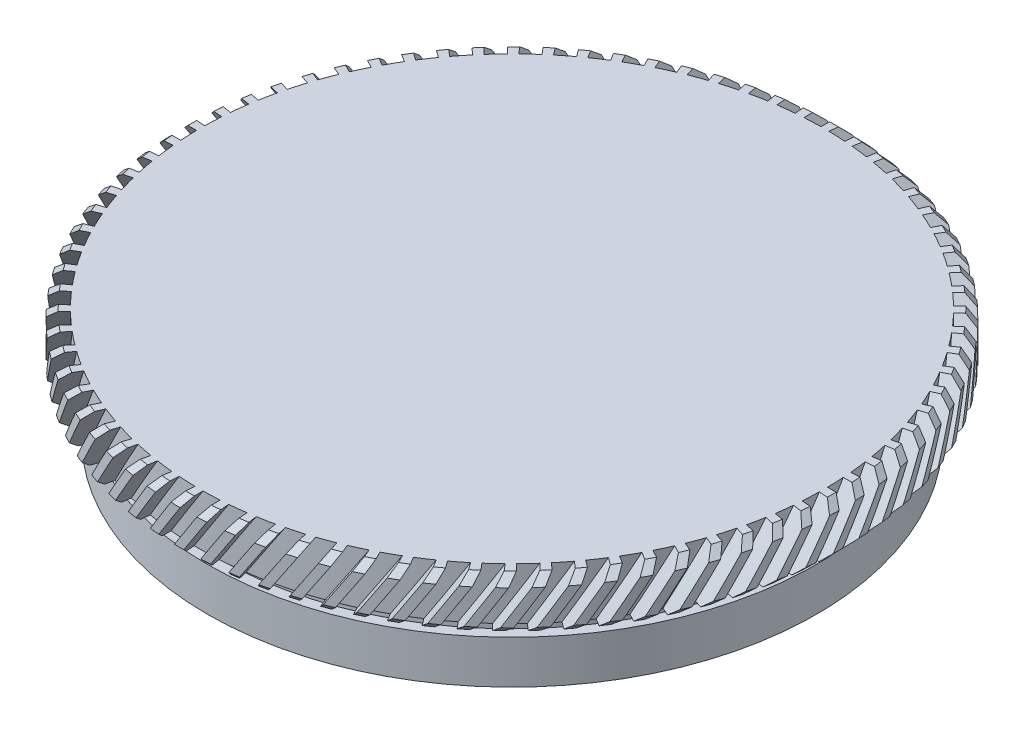
SolidWorks part; units mm, degrees
ref_plane "前视基准面" through (0, 0, 0) normal (0, 0, 1) x (1, 0, 0)
ref_plane "上视基准面" through (0, 0, 0) normal (0, 1, 0) x (1, 0, 0)
ref_plane "右视基准面" through (0, 0, 0) normal (1, 0, 0) x (0, 0, -1)
sketch "草图1" plane through (0, 0, 0) normal (0, 0, 1) x (1, 0, 0)
  line L0 (0, 66.6288) -> (0, -106.6399) construction
  line L1 (-97.6622, 0) -> (93.4292, 0) construction
  line L2 (0, 21.8713) -> (19.05, 21.8713)
  line L3 (19.05, 21.8713) -> (19.05, 18.8713)
  line L4 (17, 18.8713) -> (17, 17.8713)
  line L5 (17, 18.8713) -> (19.05, 18.8713)
  line L6 (17.6, 17.8713) -> (17.6, 15.3713)
  line L7 (17, 17.8713) -> (17.6, 17.8713)
  line L8 (15.75, 18.8713) -> (15.75, 15.3713)
  line L9 (0, 21.8713) -> (0, 18.8713)
  line L10 (15.75, 15.3713) -> (17.6, 15.3713)
  line L11 (0, 18.8713) -> (15.75, 18.8713)
  dimension "D1" = 19.05
  dimension "D2" = 3
  dimension "D3" = 17
  dimension "D4" = 17.6
  dimension "D5" = 15.75
  dimension "D6" = 1
  dimension "D7" = 2.5
revolve "旋转2" add sketch "草图1" angle 360 about L0
cosmetic thread "装饰螺纹线1" parameters "D2"=35
chamfer "倒角1" distance 0.5 angle 45 2 edges at (0, 21.8713, 19.05) (0, 18.8713, 19.05)
sketch "草图2" plane through (0, 0, 0) normal (0, 0, 1) x (1, 0, 0)
  line L0 (1.1082, 23.3033) -> (-5.3395, 13.2735)
  line L1 (1.1082, 23.3033) -> (1.7811, 22.8706)
  line L2 (-5.3395, 13.2735) -> (-4.6666, 12.8409)
  line L3 (1.7811, 22.8706) -> (-4.6666, 12.8409)
  dimension "D1" = 0.8
surface "曲面-等距1" parameters "D1"=1
extrude "切除-拉伸1" cut sketch "草图2" against normal up to surface (11.984 mm away) from offset 30
delete or keep bodies "实体-删除/保留 1" type delete bodies bodies 107
pattern_circular "阵列(圆周)2" count 80 over 360 about axis through (0, 0, 0) along (0, 1, 0) of "切除-拉伸1"
